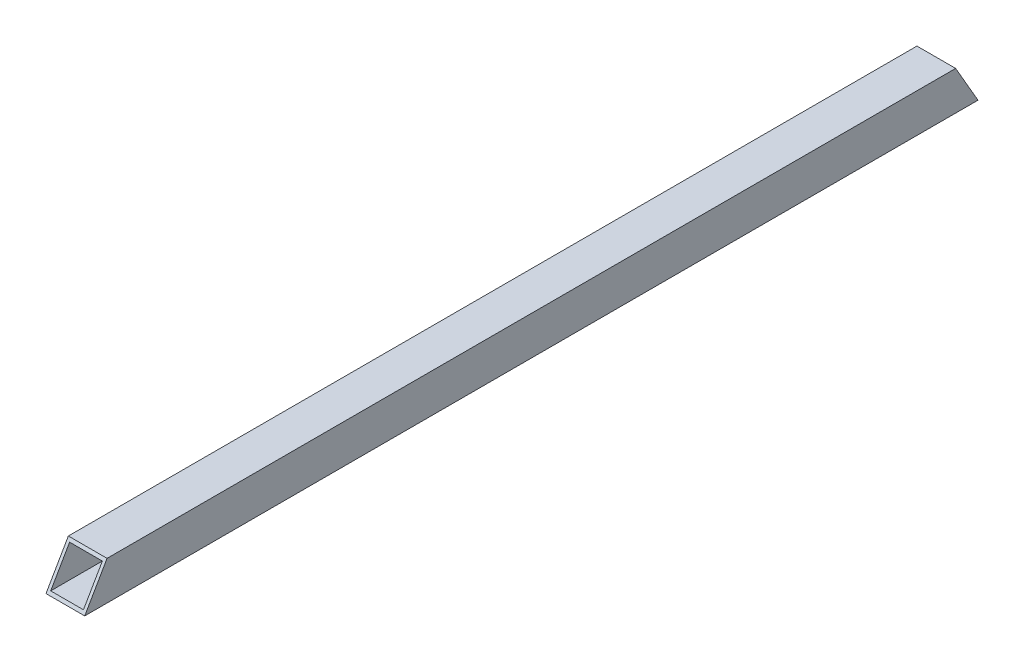
SolidWorks part; units mm, degrees
ref_plane "Front Plane" through (0, 0, 0) normal (0, 0, 1) x (1, 0, 0)
ref_plane "Top Plane" through (0, 0, 0) normal (0, 1, 0) x (1, 0, 0)
ref_plane "Right Plane" through (0, 0, 0) normal (1, 0, 0) x (0, 0, -1)
sketch "Sketch1" plane through (0, 0, 0) normal (0, 0, 1) x (1, 0, 0)
  line L0 (-6.5, 6.5) -> (6.5, 6.5)
  line L1 (-5.5, 5.5) -> (5.5, 5.5)
  line L2 (-5.5, 5.5) -> (-5.5, -5.5)
  line L3 (-5.5, -5.5) -> (5.5, -5.5)
  line L4 (5.5, 5.5) -> (5.5, -5.5)
  line L5 (-5.5, 5.5) -> (5.5, -5.5) construction
  line L6 (-5.5, -5.5) -> (5.5, 5.5) construction
  line L7 (6.5, 6.5) -> (6.5, -6.5)
  line L8 (-6.5, -6.5) -> (6.5, -6.5)
  line L9 (-6.5, 6.5) -> (-6.5, -6.5)
  point P0 (0, 0)
  dimension "D1" = 11
  dimension "11" = 11
  dimension "D2" = 1
extrude "Boss-Extrude1" add sketch "Sketch1" along normal blind 300
sketch "Sketch2" plane through (6.5, 0, 0) normal (1, 0, 0) x (0, 0, -1)
  line L0 (-292.4944, 6.5) -> (-300, -6.5)
  line L1 (-300, 6.5) -> (0, 6.5) construction
extrude "Cut-Extrude2" cut sketch "Sketch2" against normal through all both and the other way through all flip side to cut
sketch "Sketch3" plane through (6.5, 0, 0) normal (1, 0, 0) x (0, 0, -1)
  line L0 (0, -6.5) -> (-7.5056, 6.5)
  line L1 (-292.4944, 6.5) -> (0, 6.5) construction
extrude "Cut-Extrude3" cut sketch "Sketch3" against normal through all both and the other way through all flip side to cut
